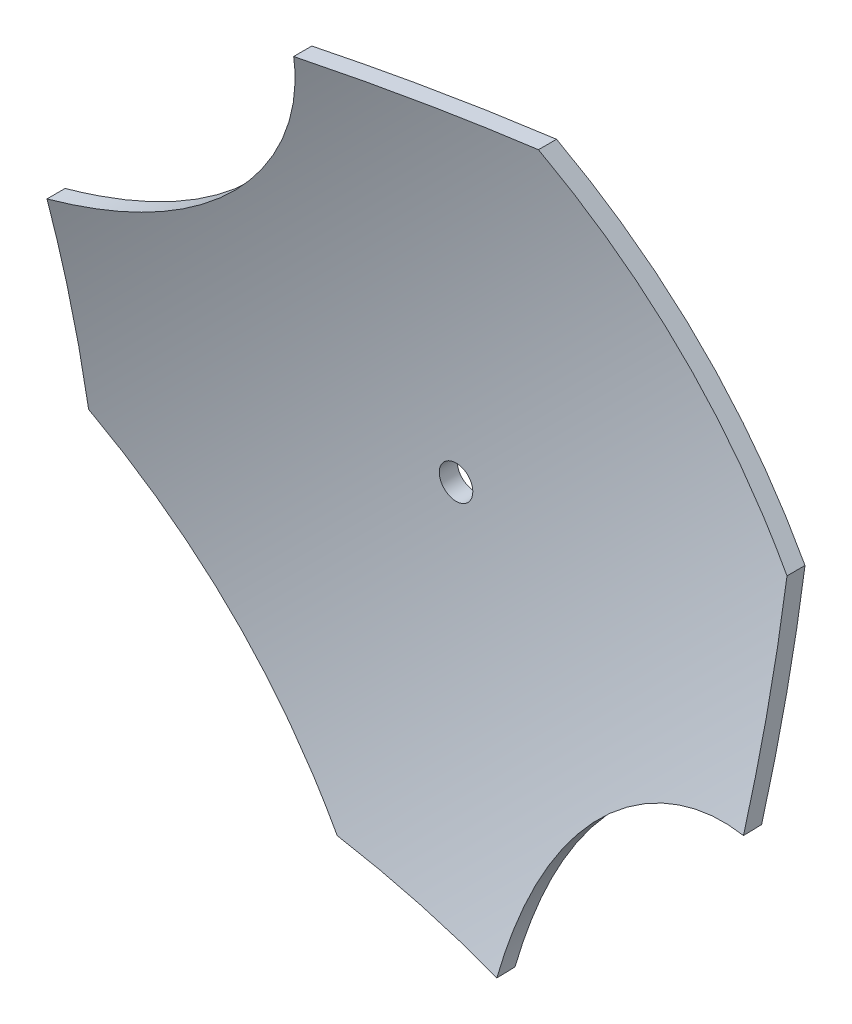
SolidWorks part; units mm, degrees
ref_plane "Front Plane" through (0, 0, 0) normal (0, 0, 1) x (1, 0, 0)
ref_plane "Top Plane" through (0, 0, 0) normal (0, 1, 0) x (1, 0, 0)
ref_plane "Right Plane" through (0, 0, 0) normal (1, 0, 0) x (0, 0, -1)
sketch "Sketch2" plane through (0, 0, 0) normal (0, 0, 1) x (1, 0, 0)
  line L0 (-84.4424, 11.0837) -> (-50.4424, -22.9163)
  line L1 (-50.4424, -22.9163) -> (-22.4424, -22.9163)
  line L2 (-84.4424, 39.0837) -> (-84.4424, 11.0837)
  line L3 (-50.4424, 73.0837) -> (-22.4424, 73.0837)
  line L4 (-22.4424, 73.0837) -> (11.5576, 39.0837)
  line L5 (11.5576, 39.0837) -> (11.5576, 11.0837)
  line L6 (11.5576, 11.0837) -> (-84.4424, 11.0837) construction
  line L7 (-84.4424, 39.0837) -> (11.5576, 39.0837) construction
  line L8 (-50.4424, 73.0837) -> (-50.4424, 39.0837) construction
  line L9 (-50.4424, 39.0837) -> (-50.4424, 11.0837) construction
  line L10 (-50.4424, 11.0837) -> (-50.4424, -22.9163) construction
  line L11 (-22.4424, -22.9163) -> (-22.4424, 11.0837) construction
  line L12 (-22.4424, 11.0837) -> (-22.4424, 39.0837) construction
  line L13 (-22.4424, 39.0837) -> (-22.4424, 73.0837) construction
  line L14 (-84.4424, 11.0837) -> (-91.5134, 4.0126) construction
  line L17 (-91.5134, 4.0126) -> (-50.4424, -22.9163) construction
  line L18 (-84.4424, 25.0837) -> (-50.4424, 25.0837) construction
  line L19 (-91.5134, 4.0126) -> (-57.5134, -29.9874) construction
  line L20 (-57.5134, -29.9874) -> (-50.4424, -22.9163) construction
  line L21 (-50.4424, 25.0837) -> (-22.4424, 25.0837) construction
  line L22 (-22.4424, 25.0837) -> (11.5576, 25.0837) construction
  line L23 (-36.4424, 73.0837) -> (-36.4424, 39.0837) construction
  line L24 (-36.4424, 39.0837) -> (-36.4424, 11.0837) construction
  line L25 (-36.4424, 11.0837) -> (-36.4424, -22.9163) construction
  arc A2 (-84.4424, 39.0837) -> (-50.4424, 73.0837) centre (-88.6843, 77.3256) ccw
  arc A3 (-22.4424, -22.9163) -> (11.5576, 11.0837) centre (15.7678, -27.1264) cw
  circle A4 centre (-36.4424, 25.0837) radius 2.2992
  dimension "D1" = 28
  dimension "D3" = 38.4413
  dimension "D4" = 38.4765
  dimension "D2" = 48.0833
  dimension "D5" = 10
extrude "Boss-Extrude1" add sketch "Sketch2" against normal blind 12
sketch "Sketch3" plane through (25.3207, 25.3207, 0) normal (0.7071, 0.7071, 0) x (0, 0, -1)
  line L0 (0, 87.3461) -> (0, 0) construction
  line L1 (12, -0.3351) -> (0, -0.3351) construction
  line L2 (12, -0.3351) -> (12, 87.3461) construction
  line L3 (12, 87.3461) -> (0, 87.3461) construction
  line L4 (0, 67.5471) -> (12, 67.5471) construction
  line L5 (0, 19.4639) -> (12, 19.4639) construction
  line L6 (12, 43.5055) -> (8.4626, 43.5055) construction
  line L7 (0, 87.3461) -> (2.5, 87.3461)
  line L8 (2.5, -0.292) -> (0, -0.3351)
  spline S0 degree 2 poles (0, -0.3351) (16.7928, 41.7689) (0, 87.3461) knots 0 0 0 1 1 1
  spline S1 degree 2 poles (2.5, -0.292) (19.2689, 41.7922) (2.5, 87.3461) knots 0 0 0 0.999526 0.999526 0.999526
  dimension "D1" = 3.5374
  dimension "D2" = 2.5
  dimension "D3" = 2.5
extrude "Cut-Extrude1" cut sketch "Sketch3" against normal through all flip side to cut
